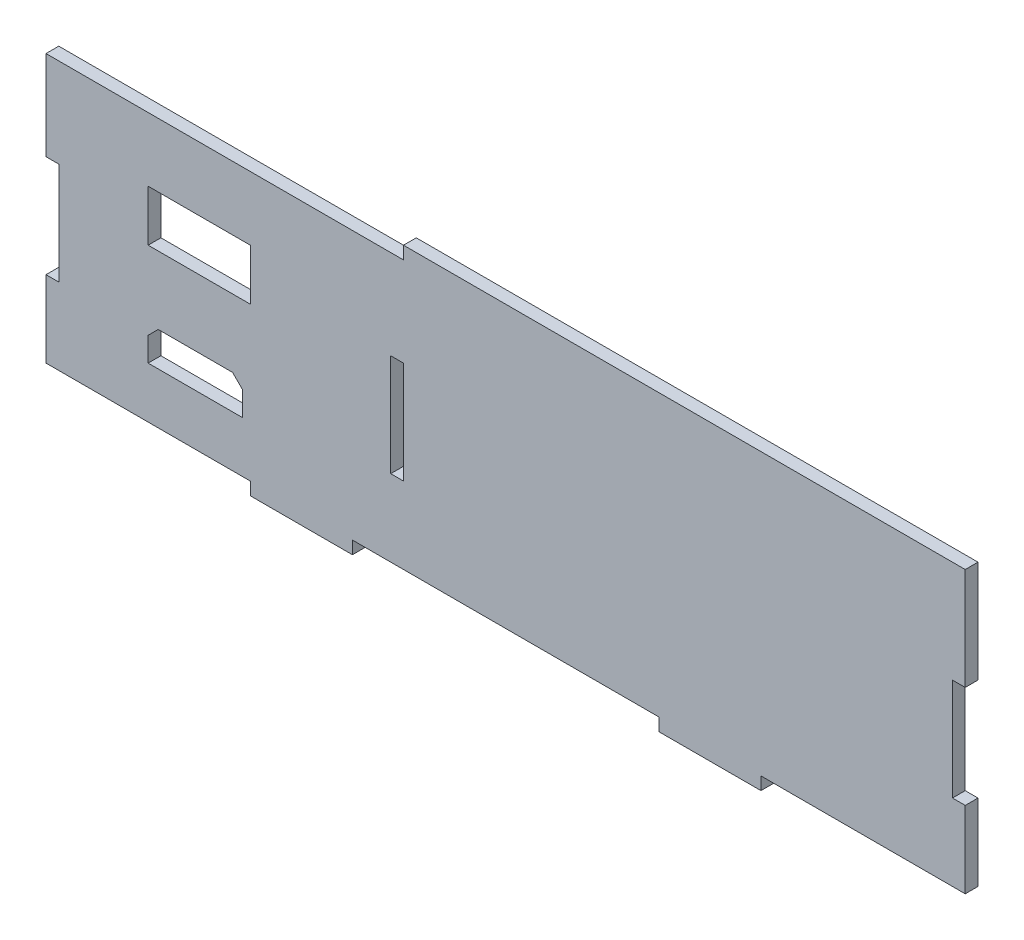
SolidWorks part; units mm, degrees
ref_plane "Front Plane" through (0, 0, 0) normal (0, 0, 1) x (1, 0, 0)
ref_plane "Top Plane" through (0, 0, 0) normal (0, 1, 0) x (1, 0, 0)
ref_plane "Right Plane" through (0, 0, 0) normal (1, 0, 0) x (0, 0, -1)
sketch "Sketch1" plane through (0, 0, 0) normal (0, 0, 1) x (1, 0, 0)
  line L0 (-114.3, 34.925) -> (-114.3, 9.525)
  line L1 (-114.3, 34.925) -> (114.3, 34.925)
  line L2 (-114.3, 9.525) -> (-111.125, 9.525)
  line L3 (-114.3, -34.925) -> (-63.5, -34.925)
  line L4 (-111.125, 9.525) -> (-111.125, -15.875)
  line L5 (-111.125, -15.875) -> (-114.3, -15.875)
  line L6 (-114.3, -15.875) -> (-114.3, -34.925)
  line L7 (114.3, 34.925) -> (114.3, 9.525)
  line L8 (114.3, 9.525) -> (111.125, 9.525)
  line L9 (111.125, 9.525) -> (111.125, -15.875)
  line L10 (111.125, -15.875) -> (114.3, -15.875)
  line L11 (114.3, -15.875) -> (114.3, -34.925)
  line L12 (-63.5, -34.925) -> (-63.5, -38.1)
  line L13 (-63.5, -38.1) -> (-38.1, -38.1)
  line L14 (-38.1, -38.1) -> (-38.1, -34.925)
  line L15 (-38.1, -34.925) -> (38.1, -34.925)
  line L16 (38.1, -34.925) -> (38.1, -38.1)
  line L17 (38.1, -38.1) -> (63.5, -38.1)
  line L18 (63.5, -38.1) -> (63.5, -34.925)
  line L19 (63.5, -34.925) -> (114.3, -34.925)
  line L21 (-28.575, 9.525) -> (-25.4, 9.525)
  line L22 (-28.575, 9.525) -> (-28.575, -15.875)
  line L23 (-28.575, -15.875) -> (-25.4, -15.875)
  line L24 (-25.4, 9.525) -> (-25.4, -15.875)
  dimension "D1" = 228.6
  dimension "D2" = 69.85
  dimension "D3" = 25.4
  dimension "D4" = 34.925
  dimension "D5" = 25.4
  dimension "D6" = 25.4
  dimension "D7" = 25.4
  dimension "D8" = 19.05
  dimension "D9" = 3.175
  dimension "D10" = 3.175
  dimension "D11" = 50.8
  dimension "D12" = 50.8
  dimension "D13" = 3.175
  dimension "D14" = 25.4
  dimension "D15" = 25.4
  dimension "D16" = 76.2
  dimension "D17" = 3.175
  dimension "D18" = 3.175
  dimension "D19" = 3.175
  dimension "D20" = 3.175
  dimension "D21" = 88.9
extrude "Boss-Extrude1" add sketch "Sketch1" along normal blind 3.175
sketch "Sketch2" plane through (0, 0, 3.175) normal (0, 0, 1) x (1, 0, 0)
  line L0 (-88.9, -16.225) -> (-86.4, -13.725)
  line L1 (-86.4, -13.725) -> (-67.9, -13.725)
  line L2 (-88.9, -16.225) -> (-88.9, -22.225)
  line L3 (-88.9, -22.225) -> (-65.4, -22.225)
  line L4 (-65.4, -16.225) -> (-65.4, -22.225)
  line L5 (-67.9, -13.725) -> (-65.4, -16.225)
  line L6 (114.3, 34.925) -> (-114.3, 34.925) construction
  line L7 (-88.9, 15.875) -> (-63.5, 15.875)
  line L8 (-88.9, 15.875) -> (-88.9, 3.175)
  line L9 (-88.9, 3.175) -> (-63.5, 3.175)
  line L10 (-63.5, 15.875) -> (-63.5, 3.175)
  line L15 (-114.3, -15.875) -> (-114.3, -34.925) construction
  line L16 (-114.3, -34.925) -> (-63.5, -34.925) construction
  point P0 (-88.9, -13.725)
  point P3 (-65.4, -13.725)
  dimension "D1" = 23.5
  dimension "D2" = 8.5
  dimension "D4" = 25.4
  dimension "D5" = 12.7
  dimension "D6" = 12.7
  dimension "D3" = 25.4
  dimension "D7" = 19.05
extrude "Cut-Extrude1" cut sketch "Sketch2" against normal through all
sketch "Sketch3" plane through (0, 0, 3.175) normal (0, 0, 1) x (1, 0, 0)
  line L1 (-114.3, 34.925) -> (-25.4, 34.925)
  line L2 (-114.3, 34.925) -> (-114.3, 31.75)
  line L3 (-114.3, 31.75) -> (-25.4, 31.75)
  line L4 (-25.4, 34.925) -> (-25.4, 31.75)
  dimension "D1" = 3.175
  dimension "D2" = 88.9
extrude "Cut-Extrude2" cut sketch "Sketch3" against normal through all
